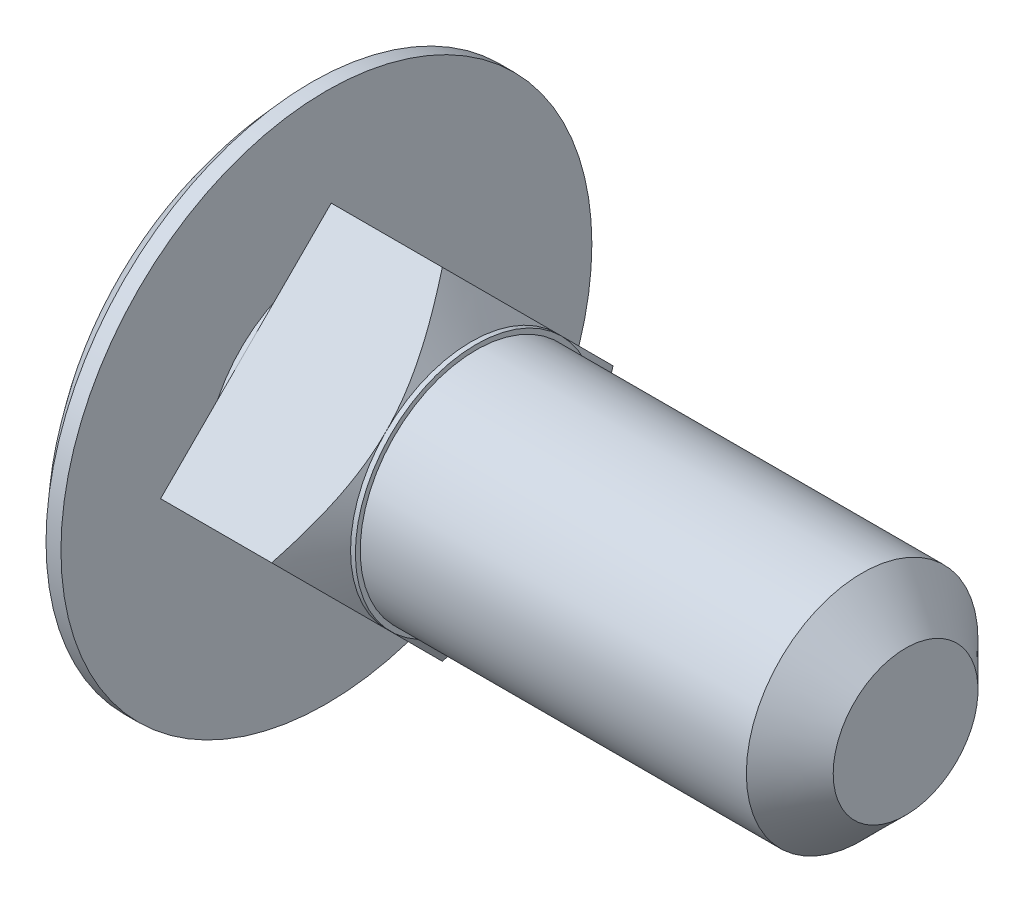
SolidWorks part; units mm, degrees
material "Серое литое железо"
ref_plane "Спереди" through (0, 0, 0) normal (0, 0, 1) x (1, 0, 0)
ref_plane "Сверху" through (0, 0, 0) normal (0, 1, 0) x (1, 0, 0)
ref_plane "Справа" through (0, 0, 0) normal (1, 0, 0) x (0, 0, -1)
sketch "Эскиз3" plane through (0, 0, 0) normal (0, 0, 1) x (1, 0, 0)
  line L0 (-123.7661, 0) -> (6064.5413, 0) construction
  line L1 (12, 0) -> (12, 1.5)
  line L2 (12, 0) -> (-2.5, 0)
  line L3 (11, 2.5) -> (0, 2.5)
  line L4 (12, 1.5) -> (11, 2.5)
  line L6 (0, 2.5) -> (0, 5.5)
  line L7 (0, 5.5) -> (-0.3095, 5.5)
  arc A0 (-0.3095, 5.5) -> (-2.5, 0) centre (5.5, 0) ccw
  point P6 (12, 2.5)
  dimension "гост R" = 8
  dimension "гост d" = 5
  dimension "гост l" = 12
  dimension "гост k" = 2.5
  dimension "гост Д" = 11
revolve "Повернуть1" add sketch "Эскиз3" angle 360 about L0
sketch "Эскиз4" plane through (0, 0, 0) normal (1, 0, 0) x (0, 0, -1)
  line L0 (0, 3.5355) -> (-3.5355, 0)
  line L1 (0, 3.5355) -> (3.5355, 0)
  line L2 (-3.5355, 0) -> (0, -3.5355)
  line L3 (3.5355, 0) -> (0, -3.5355)
  circle A0 centre (0, 0) radius 2.5 construction
extrude "Бобышка-Вытянуть1" add sketch "Эскиз4" along normal offset from surface (2.9 mm away) 3 from offset 0.1 up to face at (0, 0, 5.5) offset beyond the face yes
sketch "Эскиз5" plane through (0, 0, 0) normal (0, 0, 1) x (1, 0, 0)
  line L0 (3, 2.5) -> (2.4021, 3.5355)
  line L1 (2.4021, 3.5355) -> (3, 3.5355)
  line L2 (3, 3.5355) -> (3, 2.5)
  line L4 (3, 1.7678) -> (3, 3.5355) construction
  line L5 (11, 2.5) -> (0, 2.5) construction
  dimension "D1" = 30
revolve "Повернуть2" add sketch "Эскиз5" angle 360 about L0
combine bodies "Соединить1" operation type subtract main body 104 bodies to subtract 105
sketch "Эскиз6" plane through (12, 0, 0) normal (1, 0, 0) x (0, 0, -1)
  circle A0 centre (0, 0) radius 2.5 construction
  circle A1 centre (0, 0) radius 2.5
  circle A2 centre (0, 0) radius 2.4
  dimension "D1" = 0.1
extrude "Вырез-Вытянуть1" cut sketch "Эскиз6" against normal blind 8.9
equation "\"фф@Эскиз3\"= \"гост d@Эскиз3\" \\ 5"
